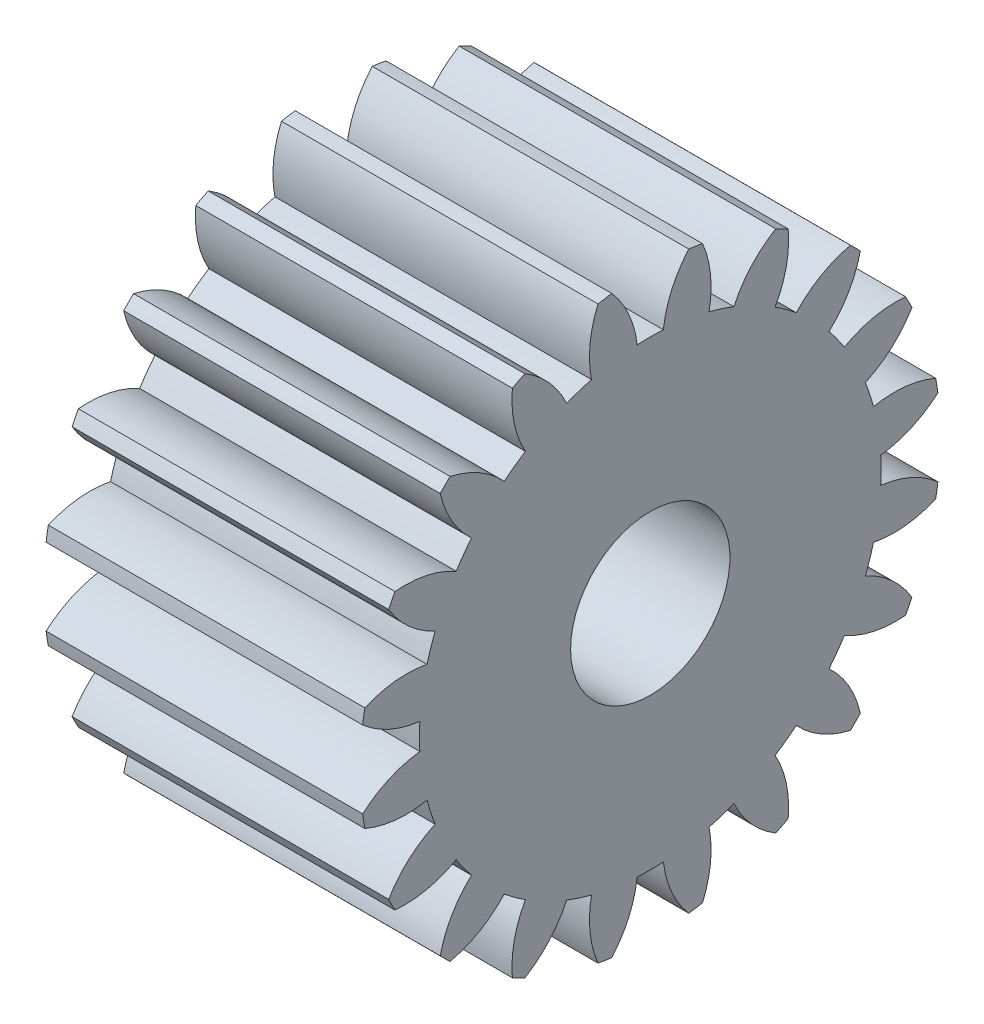
SolidWorks part; units mm, degrees
ref_plane "Plane1" through (0, 0, 0) normal (0, 0, 1) x (1, 0, 0)
ref_plane "Plane2" through (0, 0, 0) normal (0, 1, 0) x (1, 0, 0)
ref_plane "Plane3" through (0, 0, 0) normal (1, 0, 0) x (0, 0, -1)
other "Configuration Table"
sketch "HoldingSke" plane through (0, 0, 0) normal (0, 1, 0) x (1, 0, 0)
  line L0 (0, 0) -> (37.5877, -13.6808)
  line L1 (-15, 0) -> (100, 0) construction
  line L2 (0, 0) -> (-2.1039, 2.3779)
  line L3 (0, 0) -> (-11.863, 4.5341)
  line L4 (0, 0) -> (8.1152, 2.9537)
  line L5 (0, 0) -> (-46.8476, -17.4728)
  line L6 (0, 0) -> (-9.9476, -6.7116)
  line L7 (-2.1039, 2.3779) -> (8.6587, 51.2063)
  line L8 (-76.2, 54.61) -> (-73.9, 54.61)
  line L9 (-71.009, 38.7566) -> (-53.1078, 45.2721)
  line L10 (-76.2, 71.12) -> (104.1128, 71.12)
  line L11 (0, 0) -> (-12, 0)
  line L12 (-76.2, 101.6) -> (-76.113, 101.6)
  line L13 (24.9733, 27.94) -> (52.9518, 28.4284)
  line L14 (24.9733, 27.94) -> (24.9743, 27.94)
  line L15 (24.9733, 27.94) -> (100.4006, 29.5858)
  line L16 (-63.627, -2.5) -> (-12.827, -2.5)
  circle A0 centre (0, 0) radius 7.5
  circle A1 centre (0, 0) radius 21.874
  circle A2 centre (0, 0) radius 37.5
  circle A3 centre (0, 0) radius 7.5
  dimension "MHD" = 43.748
  dimension "Hub_dia" = 75
  dimension "Bore" = 15
  dimension "MBD" = 15
  dimension "Num_teeth" = 20
  dimension "Pitch" = 40
  dimension "Overall_len" = 50
  dimension "Show_teeth" = 20
  dimension "Thickness" = 12
  dimension "OAL" = 50.0005
  dimension "T_dim" = 2.3
  dimension "Ap" = 20
  dimension "H" = 19.05
  dimension "Pitch_radius" = 180.3128
  dimension "Width" = 12
  dimension "Backlash" = 0.087
  dimension "Addendum_fac" = 1
  dimension "Dedendum_fac" = 1.25
  dimension "Clearance_fac" = 0.25
  dimension "Dedendum_add" = 0.001
  dimension "Module" = 2.5
sketch "BasProSke" plane through (0, 0, 0) normal (0, 1, 0) x (1, 0, 0)
  line L0 (-10, 0) -> (60, 0) construction
  line L1 (0, 0) -> (0, 27.5)
  line L2 (0, 0) -> (30, 0)
  line L3 (30, 0) -> (30, 27.5)
  line L4 (30, 27.5) -> (0, 27.5)
  dimension "Thickness" = 30
  dimension "Diameter" = 55
revolve "Base-Revolve" add sketch "BasProSke" angle 360 about L0
sketch "TooCutSke" plane through (0, 0, 0) normal (1, 0, 0) x (0, 0, -1)
  line L1 (0, 0) -> (0, 107) construction
  line L2 (0, 0) -> (-2.1137, 24.9105) construction
  line L3 (0, 0) -> (-7.8012, 49.2549) construction
  line L4 (-2.1137, 24.9105) -> (-3.9006, 24.6275) construction
  arc A0 (1.2377, 21.839) -> (-1.2377, 21.839) centre (0, 0) ccw
  arc A1 (3.8532, 27.4852) -> (-3.8532, 27.4852) centre (0, 0) ccw
  circle A2 centre (0, 0) radius 25 construction
  circle A3 centre (0, 0) radius 23.4923 construction
  arc A4 (-1.2377, 21.839) -> (-3.8532, 27.4852) centre (-11.1689, 20.6675) ccw
  arc A5 (3.8532, 27.4852) -> (1.2377, 21.839) centre (11.1689, 20.6675) ccw
  dimension "Root_dia" = 43.748
  dimension "Overcut_dia" = 55.508
  dimension "Pitch_dia" = 50
  dimension "Base_dia" = 46.9846
  dimension "Flank_rad" = 10
  dimension "Half_ang" = 9
  dimension "Half_CT" = 1.8092
extrude "ToothCut" cut sketch "TooCutSke" along normal through all
fillet "Breaks" [suppressed] radius 0.05
fillet "RootFillets" [suppressed] radius 0.626
pattern_circular "TeethCuts" count 20 every 18 about axis through (-10, 0, 0) along (1, 0, 0) of "ToothCut", "RootFillets", "Breaks"
sketch "HubNeaOneSke" plane through (0, 0, 0) normal (-1, 0, 0) x (0, 0, 1)
  circle A0 centre (0, 0) radius 21.874
  dimension "Diameter" = 43.748
extrude "HubNearOne" [suppressed] add sketch "HubNeaOneSke" along normal blind 20.0005
sketch "HubNeaBotSke" plane through (0, 0, 0) normal (-1, 0, 0) x (0, 0, 1)
  circle A0 centre (0, 0) radius 21.874
  dimension "Diameter" = 43.748
extrude "HubNearBoth" [suppressed] add sketch "HubNeaBotSke" along normal blind 10.0003
ref_plane "FarPln" through (30, 0, 0) normal (1, 0, 0) x (0, 0, -1)
sketch "HubFarSke" plane through (30, 0, 0) normal (1, 0, 0) x (0, 0, -1)
  circle A0 centre (0, 0) radius 21.874
  dimension "Diameter" = 43.748
extrude "HubFar" [suppressed] add sketch "HubFarSke" along normal blind 10.0003
sketch "BorSke" plane through (0, 0, 0) normal (1, 0, 0) x (0, 0, -1)
  circle A0 centre (0, 0) radius 7.55
  dimension "Diameter" = 15.1
extrude "Bore" cut sketch "BorSke" along normal mid plane 100.001
sketch "KeySke" plane through (0, 0, 0) normal (1, 0, 0) x (0, 0, -1)
  line L0 (-2.5, 0) -> (-2.5, 9.8)
  line L1 (-2.5, 9.8) -> (2.5, 9.8)
  line L2 (2.5, 9.8) -> (2.5, 0)
  line L3 (0, 0) -> (0, 34) construction
  line L4 (-2.5, 0) -> (2.5, 0)
  dimension "Offset" = 9.8
  dimension "Width" = 5
extrude "Keyway" [suppressed] cut sketch "KeySke" along normal mid plane 100.001
pattern_circular "Keyway2" [suppressed] count 2 every 90 about axis through (-10, 0, 0) along (1, 0, 0)
sketch "Sketch1" plane through (0, 0, 0) normal (-1, 0, 0) x (0, 0, 1)
  circle A0 centre (0, 0) radius 20 construction
  dimension "D1" = 40
scale "Scale1" scale about centroid uniform scaling yes scale factor 0.8
equation "' \"Module@HoldingSke\" = 6.35"
equation "' \"Num_teeth@HoldingSke\" = 12"
equation "' \"Ap@HoldingSke\" =  20"
equation "' \"Ap@HoldingSke\" = 20"
equation "' \"Width@HoldingSke\" = 0.5 * 25.4"
equation "' \"Hub_dia@HoldingSke\"= 1 * 25.4"
equation "' \"Hub_dia@HoldingSke\" = 1 * 25.4"
equation "' \"Overall_len@HoldingSke\" = 1.0 * 25.4"
equation "' \"Bore@HoldingSke\" = 0.75 * 25.4"
equation "' \"T_dim@HoldingSke\" = 0.1 * 25.4"
equation "' \"Width@KeySke\" = 0.25 * 25.4"
equation "' \"Show_teeth@HoldingSke\" = 13"
equation "' \"Backlash@HoldingSke\" = 0.009 * 25.4"
equation "' \"Addendum_fac@HoldingSke\" = 1.0"
equation "' \"Dedendum_fac@HoldingSke\" = 1.25"
equation "' \"Dedendum_add@HoldingSke\" = 0.00005 * 25.4"
equation "' \"Clearance_fac@HoldingSke\" = 0.25"
equation "\"Pitch@HoldingSke\" = 1 / \"Module@HoldingSke\""
equation "\"Overcut_dia@TooCutSke\" = (\"Num_teeth@HoldingSke\" + 2 * \"Addendum_fac@HoldingSke\") / \"Pitch@HoldingSke\" + 0.002 * 25.4"
equation "\"Pitch_dia@TooCutSke\" = \"Num_teeth@HoldingSke\" / \"Pitch@HoldingSke\""
equation "\"Base_dia@TooCutSke\" = \"Num_teeth@HoldingSke\" / \"Pitch@HoldingSke\" * cos((\"Ap@HoldingSke\"  * 3.14159265 / 180))"
equation "\"Root_dia@TooCutSke\" = (\"Num_teeth@HoldingSke\" + 2) / \"Pitch@HoldingSke\" - 2 * (\"Addendum_fac@HoldingSke\" + \"Dedendum_fac@HoldingSke\") / \"Pitch@HoldingSke\" - \"Dedendum_add@HoldingSke\" * 2"
equation "\"Half_ang@TooCutSke\" = 180 / \"Num_teeth@HoldingSke\""
equation "\"Half_CT@TooCutSke\" = \"Num_teeth@HoldingSke\" / \"Pitch@HoldingSke\" * sin((3.14159265 / 2 / \"Num_teeth@HoldingSke\")) / 2 - 7 * \"Backlash@HoldingSke\" / 4"
equation "\"Flank_rad@TooCutSke\" = \"Num_teeth@HoldingSke\" / \"Pitch@HoldingSke\" / 5"
equation "\"Radius@RootFillets\" = \"Clearance_fac@HoldingSke\" / \"Pitch@HoldingSke\" + \"Dedendum_add@HoldingSke\""
equation "\"Break_rad@Breaks\" = 0.02 / \"Pitch@HoldingSke\""
equation "\"Thickness@HoldingSke\" = \"Width@HoldingSke\""
equation "\"OAL@HoldingSke\" = \"Thickness@HoldingSke\""
equation "\"MHD@HoldingSke\" = (\"Num_teeth@HoldingSke\" + 2) / \"Pitch@HoldingSke\" - 2 * (\"Addendum_fac@HoldingSke\" + \"Dedendum_fac@HoldingSke\")  / \"Pitch@HoldingSke\" - \"Dedendum_add@HoldingSke\" * 2"
equation "\"MBD@HoldingSke\" = (\"Num_teeth@HoldingSke\" + 2) / \"Pitch@HoldingSke\" - 2 * (\"Addendum_fac@HoldingSke\" + \"Dedendum_fac@HoldingSke\")  / \"Pitch@HoldingSke\" - \"Dedendum_add@HoldingSke\" * 2 - 0.002 * 25.4"
equation "\"MHD@HoldingSke\" = ((sgn( \"MHD@HoldingSke\" - \"Hub_dia@HoldingSke\" )-1)*( \"MHD@HoldingSke\" - \"Hub_dia@HoldingSke\" ))/-2+ \"Hub_dia@HoldingSke\""
equation "\"MBD@HoldingSke\" = ((sgn( \"MBD@HoldingSke\" - \"Bore@HoldingSke\" )-1)*( \"MBD@HoldingSke\" - \"Bore@HoldingSke\" ))/-2+ \"Bore@HoldingSke\""
equation "\"OAL@HoldingSke\" = ((sgn( \"OAL@HoldingSke\" - \"Overall_len@HoldingSke\" )+1)*( \"OAL@HoldingSke\" - \"Overall_len@HoldingSke\" ))/2 + \"Overall_len@HoldingSke\" + 0.000002 * 25.4"
equation "\"Num_teeth@TeethCuts\" = int( \"Show_teeth@HoldingSke\" ) + 1"
equation "\"Num_teeth@TeethCuts\" = ((sgn( \"Num_teeth@TeethCuts\" - \"Num_teeth@HoldingSke\" )-1)*( \"Num_teeth@TeethCuts\" - \"Num_teeth@HoldingSke\" ))/-2+ \"Num_teeth@HoldingSke\""
equation "\"Num_teeth@TeethCuts\" = ((sgn( \"Num_teeth@TeethCuts\" - 2.0)+1)*( \"Num_teeth@TeethCuts\" - 2.0))/2 +2.0"
equation "\"Angle@TeethCuts\" = 360.0 / \"Num_teeth@HoldingSke\""
equation "\"Diameter@BasProSke\" = (\"Num_teeth@HoldingSke\" + 2 * \"Addendum_fac@HoldingSke\") / \"Pitch@HoldingSke\""
equation "' \"Fillet_rad@BasProSke\" =  \"Thickness@HoldingSke\" * 0.05"
equation "' \"Fillet_rad@BasProSke\" = \"Thickness@HoldingSke\" * 0.05"
equation "\"MHD@HoldingSke\" = ((sgn( \"MHD@HoldingSke\" - \"Root_dia@TooCutSke\" )-1)*( \"MHD@HoldingSke\" - \"Root_dia@TooCutSke\" ))/-2+ \"Root_dia@TooCutSke\""
equation "\"Diameter@HubNeaOneSke\" = \"MHD@HoldingSke\""
equation "\"Length@HubNearOne\" = \"OAL@HoldingSke\" - \"Thickness@BasProSke\""
equation "\"Diameter@HubNeaBotSke\" = \"MHD@HoldingSke\""
equation "\"Length@HubNearBoth\" = ( \"OAL@HoldingSke\" - \"Thickness@BasProSke\" ) / 2.0"
equation "\"Thickness@FarPln\" = \"Thickness@BasProSke\""
equation "\"Diameter@HubFarSke\" = \"MHD@HoldingSke\""
equation "\"Length@HubFar\" = ( \"OAL@HoldingSke\" - \"Thickness@BasProSke\" ) / 2.0"
equation "\"Diameter@BorSke\"=1.51"
equation "\"D1@Bore\" = \"OAL@HoldingSke\" * 2.0"
equation "\"D1@Keyway\" = \"OAL@HoldingSke\" * 2.0"
equation "\"Offset@KeySke\" = \"T_dim@HoldingSke\" + \"MBD@HoldingSke\" / 2.0"
